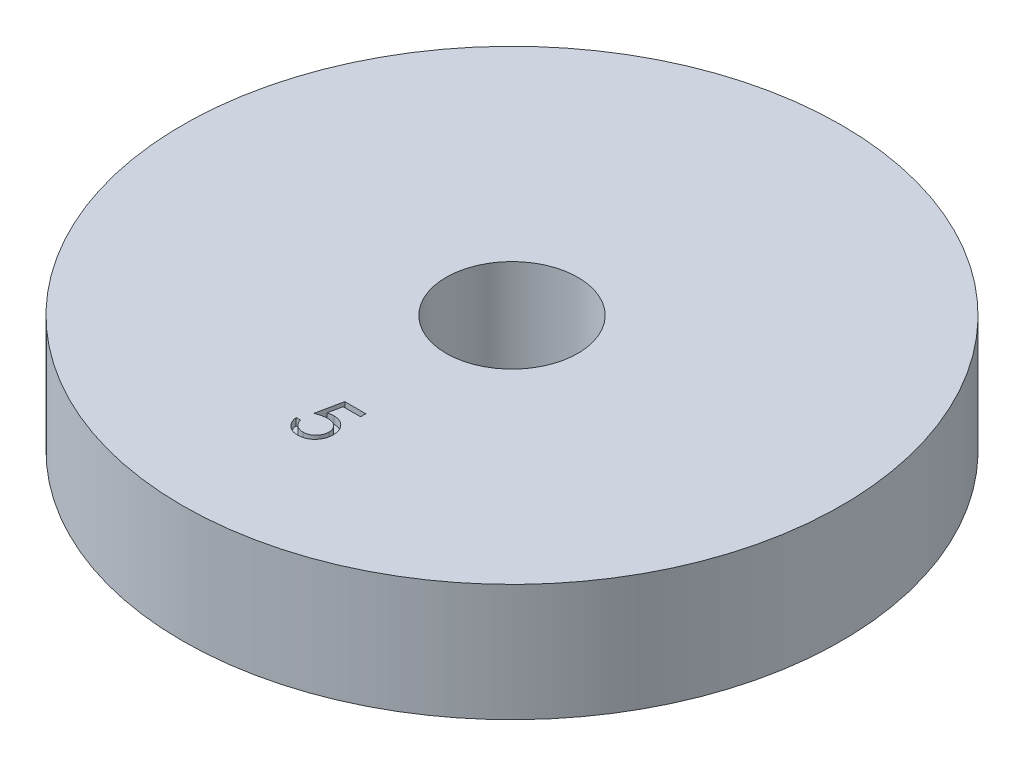
SolidWorks part; units mm, degrees
material "Laiton"
ref_plane "Plan de face" through (0, 0, 0) normal (0, 0, 1) x (1, 0, 0)
ref_plane "Plan de dessus" through (0, 0, 0) normal (0, 1, 0) x (1, 0, 0)
ref_plane "Plan de droite" through (0, 0, 0) normal (1, 0, 0) x (0, 0, -1)
sketch "Esquisse1" plane through (0, 0, 0) normal (0, 1, 0) x (1, 0, 0)
  circle A0 centre (0, 0) radius 22.5
  dimension "D1" = 45
extrude "Boss.-Extru.1" add sketch "Esquisse1" along normal blind 8
sketch "Esquisse2" plane through (0, 8, 0) normal (0, 1, 0) x (1, 0, 0)
  circle A0 centre (0, 0) radius 4.5
  dimension "D1" = 9
extrude "Enlèv. mat.-Extru.1" cut sketch "Esquisse2" against normal blind 8
sketch "Esquisse3" plane through (0, 8, 0) normal (0, 1, 0) x (1, 0, 0)
  line L0 (0, 0) -> (0, -22.5) construction
  circle A0 centre (0, 0) radius 22.5 construction
  text T0 "5"
extrude "Enlèv. mat.-Extru.2" cut sketch "Esquisse3" against normal blind 0.5
